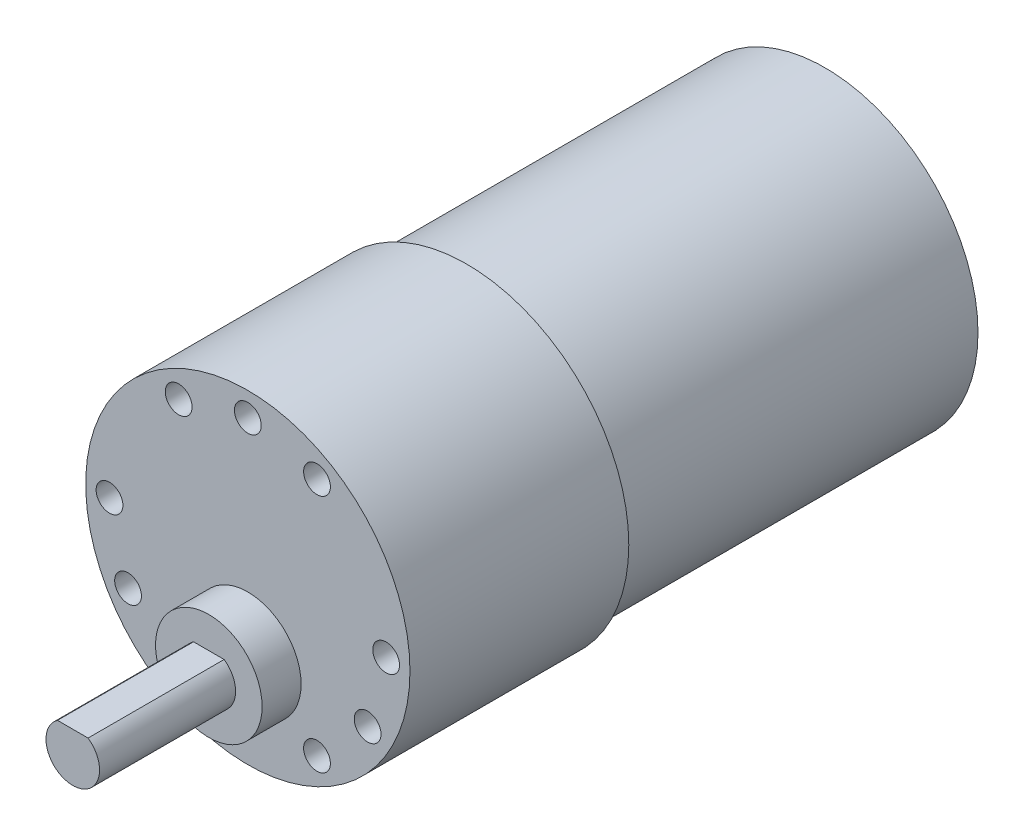
SolidWorks part; units mm, degrees
ref_plane "Front Plane" through (0, 0, 0) normal (0, 0, 1) x (1, 0, 0)
ref_plane "Top Plane" through (0, 0, 0) normal (0, 1, 0) x (1, 0, 0)
ref_plane "Right Plane" through (0, 0, 0) normal (1, 0, 0) x (0, 0, -1)
sketch "Sketch1" plane through (0, 0, 0) normal (0, 0, 1) x (1, 0, 0)
  circle A0 centre (0, 0) radius 18.161
  dimension "D1" = 36.322
extrude "Boss-Extrude1" add sketch "Sketch1" along normal blind 24.511
sketch "Sketch5" plane through (0, 0, 24.511) normal (0, 0, 1) x (1, 0, 0)
  circle A0 centre (0, -7.366) radius 5.969
  dimension "D1" = 11.938
  dimension "D2" = 7.366
extrude "Boss-Extrude5" add sketch "Sketch5" along normal blind 4.3688
sketch "Sketch6" plane through (0, 0, 28.8798) normal (0, 0, 1) x (1, 0, 0)
  line L0 (-1.7157, -4.905) -> (1.7157, -4.905)
  arc A0 (-1.7157, -4.905) -> (1.7157, -4.905) centre (0, -7.366) ccw
  dimension "D1" = 6
  dimension "D2" = 2.461
extrude "Boss-Extrude6" add sketch "Sketch6" along normal blind 15.24
sketch "Sketch9" plane through (0, 0, 24.511) normal (0, 0, 1) x (1, 0, 0)
  line L0 (0, 0) -> (0, 15.494) construction
  circle A0 centre (0, 0) radius 15.494 construction
  dimension "D1" = 30.988
hole_wizard "Ø3.0mm Dowel Hole1" positions "Sketch11" profile "Sketch12" hole size "Ø3.0" standard "ANSI Metric"
sketch "Sketch11" plane through (0, 0, 24.511) normal (0, 0, 1) x (1, 0, 0)
  point P0 (0, 15.494)
sketch "Sketch12" plane through (0, 15.494, 24.511) normal (1, 0, 0) x (0, -1, 0)
  line L0 (0, 0) -> (0, 11.0613)
  line L1 (0, 11.0613) -> (1.5, 10.16)
  line L2 (1.5, 10.16) -> (1.5, 0)
  line L5 (1.5, 0) -> (0, 0)
  line L10 (0, 11.0613) -> (-1.5, 10.16) construction
  line L11 (0, -6.35) -> (0, 107.95) construction
  dimension "Hole Dia." = 3
  dimension "Hole Depth" = 10.16
  dimension "Drill Angle" = 118
pattern_circular "CirPattern2" count 12 over 360 about axis through (0, 0, 0) along (0, 0, 1) skipping 2, 6, 10 of "Ø3.0mm Dowel Hole1"
sketch "Sketch2" plane through (0, 0, 0) normal (0, 0, -1) x (-1, 0, 0)
  circle A0 centre (0, 0) radius 17.145
  dimension "D1" = 34.29
extrude "Boss-Extrude2" add sketch "Sketch2" along normal blind 40.132
sketch "Sketch3" plane through (0, 0, -40.132) normal (0, 0, -1) x (-1, 0, 0)
  circle A0 centre (0, 0) radius 3.048
  dimension "D1" = 6.096
extrude "Boss-Extrude3" add sketch "Sketch3" along normal blind 3.81
sketch "Sketch13" plane through (0, 0, -40.132) normal (0, 0, -1) x (-1, 0, 0)
  circle A0 centre (0, 0) radius 16.637
  dimension "D1" = 33.274
extrude "Cut-Extrude1" cut sketch "Sketch13" against normal blind 1.016
sketch "Sketch14" plane through (0, 0, -39.116) normal (0, 0, -1) x (-1, 0, 0)
  line L0 (0, 0) -> (2.9583, -11.0405) construction
  line L1 (0, 0) -> (-6.5307, -7.783) construction
  circle A0 centre (0, 0) radius 11.43 construction
  circle A1 centre (0, 0) radius 10.16 construction
  dimension "D1" = 22.86
  dimension "D2" = 20.32
ref_plane "Plane1" through (0, 0, 0) normal (0.766, 0.6428, 0) x (0.6428, -0.766, 0)
ref_plane "Plane2" through (0, 0, 0) normal (0.9659, -0.2588, 0) x (-0.2588, -0.9659, 0)
sketch "Sketch15" plane through (0, 0, 0) normal (0.766, 0.6428, 0) x (0.6428, -0.766, 0)
  line L0 (8.89, 39.116) -> (8.89, 44.196)
  line L3 (10.16, 39.116) -> (-10.16, 39.116) construction
  line L4 (8.89, 44.196) -> (11.43, 44.196)
  line L5 (11.43, 44.196) -> (11.43, 39.116)
  line L6 (11.43, 39.116) -> (-11.43, 39.116) construction
  line L7 (11.43, 39.116) -> (8.89, 39.116)
  circle A0 centre (10.16, 42.926) radius 0.4445
  dimension "D4" = 0.889
  dimension "D1" = 5.08
  dimension "D2" = 2.54
  dimension "D3" = 1.27
  dimension "D5" = 1.27
  dimension "D6" = 1.27
extrude "Boss-Extrude7" add sketch "Sketch15" along normal mid plane 0.508
sketch "Sketch16" plane through (0, 0, 0) normal (0.9659, -0.2588, 0) x (-0.2588, -0.9659, 0)
  line L0 (12.7, 39.116) -> (12.7, 44.196)
  line L1 (12.7, 44.196) -> (10.16, 44.196)
  line L2 (10.16, 44.196) -> (10.16, 39.116)
  line L3 (10.16, 39.116) -> (-10.16, 39.116) construction
  line L4 (10.16, 39.116) -> (12.7, 39.116)
  circle A0 centre (11.43, 42.926) radius 0.6786
  dimension "D1" = 1.27
  dimension "D2" = 2.54
  dimension "D3" = 5.08
  dimension "D4" = 1.27
  dimension "D5" = 1.27
extrude "Boss-Extrude8" add sketch "Sketch16" along normal mid plane 0.508
